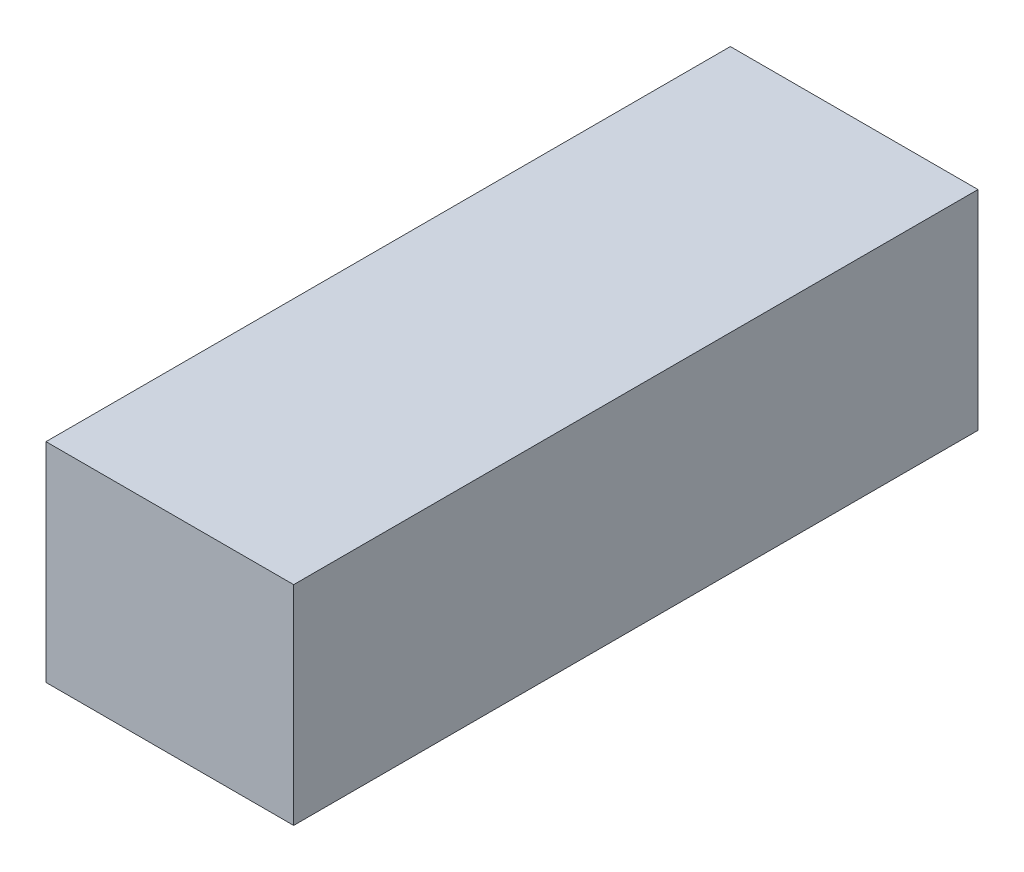
SolidWorks part; units mm, degrees
ref_plane "Front Plane" through (0, 0, 0) normal (0, 0, 1) x (1, 0, 0)
ref_plane "Top Plane" through (0, 0, 0) normal (0, 1, 0) x (1, 0, 0)
ref_plane "Right Plane" through (0, 0, 0) normal (1, 0, 0) x (0, 0, -1)
sketch "Sketch1" plane through (0, 0, 0) normal (0, 0, 1) x (1, 0, 0)
  line L1 (-34.5956, -7.5698) -> (3.4044, -7.5698)
  line L2 (-34.5956, -7.5698) -> (-34.5956, 24.4302)
  line L3 (-34.5956, 24.4302) -> (3.4044, 24.4302)
  line L4 (3.4044, -7.5698) -> (3.4044, 24.4302)
  dimension "D1" = 32
  dimension "D2" = 38
extrude "Boss-Extrude1" add sketch "Sketch1" along normal blind 105
